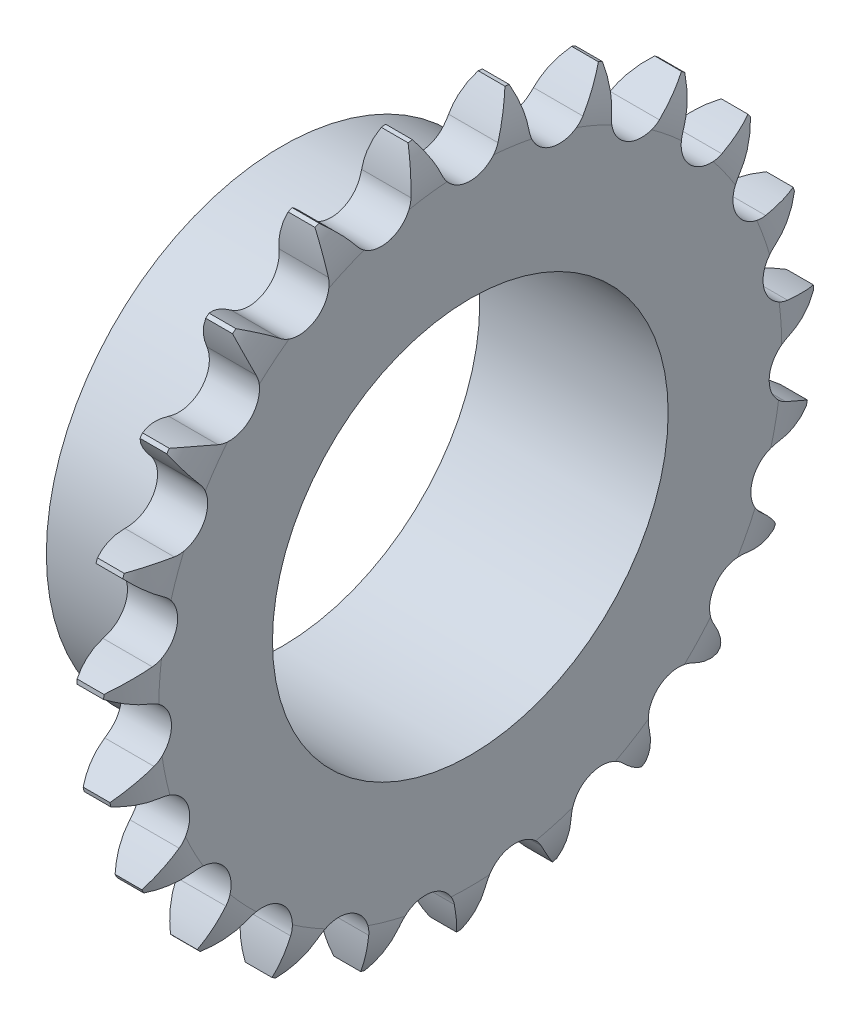
SolidWorks part; units mm, degrees
ref_plane "Plane1" through (0, 0, 0) normal (0, 0, 1) x (1, 0, 0)
ref_plane "Plane2" through (0, 0, 0) normal (0, 1, 0) x (1, 0, 0)
ref_plane "Plane3" through (0, 0, 0) normal (1, 0, 0) x (0, 0, -1)
sketch "Clipboard" plane through (0, 0, 0) normal (0, 1, 0) x (1, 0, 0)
  line L0 (0, 0) -> (8.7678, -3.7217)
  line L1 (-15, 0) -> (100, 0) construction
  line L2 (0, 0) -> (-0.8203, 0.9272)
  line L3 (0, 0) -> (-8.8973, 3.4006)
  line L4 (0, 0) -> (2.8536, 1.2113)
  line L5 (0, 0) -> (-18.7391, -6.9891)
  line L6 (0, 0) -> (-4.4098, -2.9753)
  line L7 (-0.8203, 0.9272) -> (17.451, 9.0621)
  line L8 (-76.2, 38.1) -> (-72.9, 38.1)
  line L9 (-73.3242, 40.7328) -> (-72.926, 40.7699)
  line L10 (-73.4529, 9.1872) -> (-63.2129, 9.1872)
  circle A0 centre (0, 0) radius 3.175
  circle A1 centre (0, 0) radius 25
  circle A2 centre (0, 0) radius 25
  dimension "Dr" = 6.35
  dimension "MHD" = 50
  dimension "Hub_dia" = 50
  dimension "Num_teeth" = 23
  dimension "Pitch" = 9.525
  dimension "Width" = 3.1
  dimension "Side_relief" = 1.238
  dimension "Side_radius" = 9.525
  dimension "Overall_len" = 20
  dimension "Show_teeth" = 23
  dimension "Thickness" = 5.3196
  dimension "OAL" = 20.0005
  dimension "T_dim" = 3.3
  dimension "Fillet_rad" = 0.4
  dimension "Face_width" = 5.32
  dimension "Num_strands" = 1
  dimension "Transv_pitch" = 10.24
  dimension "Plate_wid" = 8.26
sketch "BasProSke" plane through (0, 0, 0) normal (0, 1, 0) x (1, 0, 0)
  line L0 (-10, 0) -> (60, 0) construction
  line L1 (0, 0) -> (0, 33.0578)
  line L2 (0, 0) -> (5.3196, 0)
  line L3 (5.3196, 0) -> (5.3196, 33.0578)
  line L4 (4.0816, 37.7536) -> (1.238, 37.7536)
  arc A0 (0, 33.0578) -> (1.238, 37.7536) centre (9.525, 33.0578) cw
  arc A1 (5.3196, 33.0578) -> (4.0816, 37.7536) centre (-4.2054, 33.0578) ccw
  dimension "Thickness" = 5.3196
  dimension "D1" = 9.525
  dimension "G1" = 1.238
  dimension "G2" = 1.238
  dimension "Diameter" = 75.5073
revolve "Base-Revolve" add sketch "BasProSke" angle 360 about L0
sketch "TooCutSke" plane through (0, 0, 0) normal (1, 0, 0) x (0, 0, -1)
  line L0 (0, 35.0073) -> (2.9742, 33.8083) construction
  line L1 (0, 0) -> (0, 107) construction
  line L2 (0, 35.0073) -> (-10, 35.0073) construction
  line L3 (0, 35.0073) -> (-2.9742, 33.8083) construction
  arc A0 (2.9742, 33.8083) -> (5.2383, 37.8933) centre (20.6424, 26.6854) cw
  arc A1 (2.9742, 33.8083) -> (-2.9742, 33.8083) centre (0, 35.0073) cw
  arc A2 (-2.9742, 33.8083) -> (-5.2383, 37.8933) centre (-20.6424, 26.6854) ccw
  arc A3 (5.2383, 37.8933) -> (-5.2383, 37.8933) centre (0, 0) ccw
  dimension "R1" = 3.2067
  dimension "R2" = 19.05
  dimension "Overcut" = 38.2536
  dimension "Seat_radius" = 35.0073
  dimension "X" = 136.087
extrude "ToothCut" cut sketch "TooCutSke" along normal through all
pattern_circular "TeethCuts" count 23 every 15.652 about axis through (-10, 0, 0) along (1, 0, 0) of "ToothCut"
sketch "HubNeaOneSke" plane through (0, 0, 0) normal (-1, 0, 0) x (0, 0, 1)
  circle A0 centre (0, 0) radius 25
  dimension "Diameter" = 50
extrude "HubNearOne" add sketch "HubNeaOneSke" along normal blind 14.6809
fillet "HubNearOneFillet" radius 0.4 1 edges at (0, 0, -25)
sketch "HubNeaBotSke" plane through (0, 0, 0) normal (-1, 0, 0) x (0, 0, 1)
  circle A0 centre (0, 0) radius 25
  dimension "Diameter" = 50
extrude "HubNearBoth" [suppressed] add sketch "HubNeaBotSke" along normal blind 7.3404
fillet "HubNearBothFillet" [suppressed] radius 0.4
ref_plane "FarPln" through (5.3196, 0, 0) normal (1, 0, 0) x (0, 0, -1)
sketch "HubFarSke" plane through (5.3196, 0, 0) normal (1, 0, 0) x (0, 0, -1)
  circle A0 centre (0, 0) radius 25
  dimension "Diameter" = 50
extrude "HubFar" [suppressed] add sketch "HubFarSke" along normal blind 7.3404
fillet "HubFarFillet" [suppressed] radius 0.4
sketch "BorSke" plane through (0, 0, 0) normal (1, 0, 0) x (0, 0, -1)
  circle A0 centre (0, 0) radius 21
  dimension "Diameter" = 42
extrude "Bore" cut sketch "BorSke" along normal mid plane 40.001
sketch "KeySke" plane through (0, 0, 0) normal (1, 0, 0) x (0, 0, -1)
  line L0 (-6, 0) -> (-6, 24.3)
  line L1 (-6, 24.3) -> (6, 24.3)
  line L2 (6, 24.3) -> (6, 0)
  line L3 (0, 0) -> (0, 34) construction
  line L4 (-6, 0) -> (6, 0)
  dimension "Offset" = 24.3
  dimension "Width" = 12
extrude "Keyway" [suppressed] cut sketch "KeySke" along normal mid plane 40.001
pattern_circular "Keyway2" [suppressed] count 2 every 90 about axis through (-10, 0, 0) along (1, 0, 0)
equation "' \"Pitch@Clipboard\" = 12.7"
equation "' \"Num_strands@Clipboard\" = 1"
equation "' \"Num_teeth@Clipboard\" = 9"
equation "' \"Hub_dia@Clipboard\" = 50"
equation "' \"Overall_len@Clipboard\" = 3"
equation "' \"Diameter@BorSke\" = 12"
equation "' \"T_dim@Clipboard\" = 1"
equation "' \"Width@KeySke\" = 2"
equation "' \"Dr@Clipboard\" = 8.51"
equation "' \"Face_width@Clipboard\" = 7.2"
equation "' \"Side_radius@Clipboard\" = 12.7"
equation "' \"Side_relief@Clipboard\" = 1.27"
equation "' \"Transv_pitch@Clipboard\" = 13.92"
equation "' \"Show_teeth@Clipboard\" = 9"
equation "' \"Fillet_rad@Clipboard\" = 0.6"
equation "' \"Plate_wid@Clipboard\" = 11.8"
equation "\"Num_teeth@Clipboard\" = int( \"Num_teeth@Clipboard\" )"
equation "\"Num_teeth@Clipboard\" = ((sgn( \"Num_teeth@Clipboard\" - 5.0)+1)*( \"Num_teeth@Clipboard\" - 5.0))/2 +5.0"
equation "\"Num_teeth@Clipboard\" = ((sgn( \"Num_teeth@Clipboard\" - 200.0)-1)*( \"Num_teeth@Clipboard\" - 200.0))/-2 +200.0"
equation "\"MHD@Clipboard\" = \"Pitch@Clipboard\" * (1.0 / tan(3.14159265 / \"Num_teeth@Clipboard\" )) - 1.04 * \"Plate_wid@Clipboard\" - 0.76"
equation "\"Thickness@Clipboard\"  = \"Face_width@Clipboard\" + (\"Num_strands@Clipboard\" - 1) * \"Transv_pitch@Clipboard\""
equation "\"OAL@Clipboard\" = \"Thickness@Clipboard\" + 2 * \"Fillet_rad@Clipboard\" + 1"
equation "\"MHD@Clipboard\" = ((sgn( \"MHD@Clipboard\" - \"Hub_dia@Clipboard\" )-1)*( \"MHD@Clipboard\" - \"Hub_dia@Clipboard\" ))/-2+ \"Hub_dia@Clipboard\""
equation "\"OAL@Clipboard\" = ((sgn( \"OAL@Clipboard\" - \"Overall_len@Clipboard\" )+1)*( \"OAL@Clipboard\" - \"Overall_len@Clipboard\" ))/2 + \"Overall_len@Clipboard\" + 0.0005"
equation "\"Num_teeth@TeethCuts\" = int( \"Show_teeth@Clipboard\" ) + 1"
equation "\"Num_teeth@TeethCuts\" = ((sgn( \"Num_teeth@TeethCuts\" - \"Num_teeth@Clipboard\" )-1)*( \"Num_teeth@TeethCuts\" - \"Num_teeth@Clipboard\" ))/-2+ \"Num_teeth@Clipboard\""
equation "\"Num_teeth@TeethCuts\" = ((sgn( \"Num_teeth@TeethCuts\" - 2.0)+1)*( \"Num_teeth@TeethCuts\" - 2.0))/2 +2.0"
equation "\"Angle@TeethCuts\" = 360.0 / \"Num_teeth@Clipboard\""
equation "\"Seat_radius@TooCutSke\" = ( \"Pitch@Clipboard\" / 2.0) / sin(3.14159265 / \"Num_teeth@Clipboard\" ) - \"Dr@Clipboard\" / 2.0 + \"Dr@Clipboard\" * 0.505"
equation "\"R1@TooCutSke\"  = \"Dr@Clipboard\" * 0.505"
equation "\"X@TooCutSke\" = 140.0 - (90.0 / \"Num_teeth@Clipboard\")"
equation "\"R2@TooCutSke\" = 0.12 * \"Dr@Clipboard\" * ( \"Num_teeth@Clipboard\" + 2.0)"
equation "\"Overcut@TooCutSke\" = 0.5 + 0.625 * \"Pitch@Clipboard\" - 0.5 * \"Dr@Clipboard\"  +  \"Pitch@Clipboard\" / 2.0 / sin(3.14159265 / \"Num_teeth@Clipboard\" )"
equation "\"Diameter@BasProSke\" = 2.0 * ( 0.625 * \"Pitch@Clipboard\" - 0.5 * \"Dr@Clipboard\"  +  \"Pitch@Clipboard\" / 2.0 / sin(3.14159265 / \"Num_teeth@Clipboard\" ))"
equation "\"Thickness@BasProSke\"  = \"Thickness@Clipboard\""
equation "\"G1@BasProSke\" =  \"Side_relief@Clipboard\""
equation "\"G2@BasProSke\" =  \"Side_relief@Clipboard\""
equation "\"D1@BasProSke\" =  \"Side_radius@Clipboard\""
equation "\"Diameter@HubNeaOneSke\" = \"MHD@Clipboard\""
equation "\"Length@HubNearOne\" = \"OAL@Clipboard\" - \"Thickness@BasProSke\""
equation "\"Diameter@HubNeaBotSke\" = \"MHD@Clipboard\""
equation "\"Length@HubNearBoth\" = ( \"OAL@Clipboard\" - \"Thickness@BasProSke\" ) / 2.0"
equation "\"D1@HubNearOneFillet\" = \"Fillet_rad@Clipboard\""
equation "\"D1@HubNearBothFillet\" = \"Fillet_rad@Clipboard\""
equation "\"Thickness@FarPln\" = \"Thickness@BasProSke\""
equation "\"Diameter@HubFarSke\" = \"MHD@Clipboard\""
equation "\"Length@HubFar\" = ( \"OAL@Clipboard\" - \"Thickness@BasProSke\" ) / 2.0"
equation "\"D1@HubFarFillet\" = \"Fillet_rad@Clipboard\""
equation "\"D1@Bore\" = \"OAL@Clipboard\" * 2.0"
equation "\"D1@Keyway\" = \"OAL@Clipboard\" * 2.0"
equation "\"Offset@KeySke\" = \"T_dim@Clipboard\" + \"Diameter@BorSke\" / 2.0"
